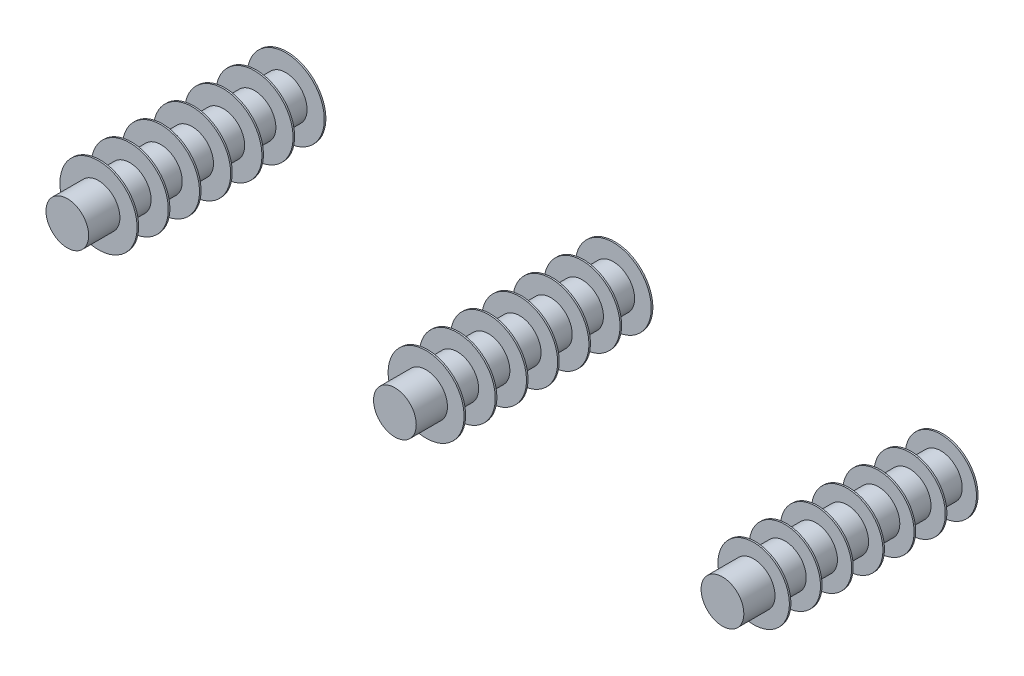
SolidWorks part; units mm, degrees
ref_plane "Alzado" through (0, 0, 0) normal (0, 0, 1) x (1, 0, 0)
ref_plane "Planta" through (0, 0, 0) normal (0, 1, 0) x (1, 0, 0)
ref_plane "Vista lateral" through (0, 0, 0) normal (1, 0, 0) x (0, 0, -1)
sketch "Croquis1" plane through (0, 0, 0) normal (0, 0, 1) x (1, 0, 0)
  line L0 (0, 0) -> (210, 0) construction
  line L1 (210, 0) -> (420, 0) construction
  circle A0 centre (0, 0) radius 13.7
  circle A1 centre (210, 0) radius 13.7
  circle A2 centre (210, 0) radius 13.7
  dimension "D1" = 27.4
  dimension "D3" = 27.4
  dimension "D2" = 210
  dimension "D4" = 210
sketch3d "Croquis3D1"
  line L0 (0, 0, 0) -> (0, 0, 170)
  line L1 (30, 0, 200) -> (145.0002, 0, 200)
  line L2 (175.0002, 0, 230) -> (175.0002, 0, 500)
  line L3 (175.0002, -20, 520) -> (175.0002, -156.8001, 520)
  arc A0 (0, 0, 170) -> (30, 0, 200) centre (30, 0, 170) ccw
  arc A1 (145.0002, 0, 200) -> (175.0002, 0, 230) centre (145.0002, 0, 230) ccw
  arc A2 (175.0002, 0, 500) -> (175.0002, -20, 520) centre (175.0002, -20, 500) ccw
  point P10 (0, 0, 200)
  point P11 (30, 30, 170)
  point P14 (175.0002, 0, 200)
  point P15 (145.0002, -30, 230)
  point P19 (175.0002, 0, 520)
  point P20 (195.0002, -20, 500)
  dimension "D1" = 30
  dimension "D2" = 20
  dimension "D3" = 175.0002
  dimension "D4" = 200
  dimension "D5" = 320
sweep "Barrer5" add path "Croquis3D1" circular profile diameter 27.4 parameters "D3"=27.4
sketch "Croquis14" plane through (0, 0, 0) normal (0, 0, 1) x (1, 0, 0)
  circle A0 centre (210, 0) radius 13.7
sketch3d "Croquis3D2"
  line L0 (210, 0, 0) -> (210, 0, 499.997)
  line L1 (210, -20, 519.997) -> (210, -153.4253, 519.997)
  arc A0 (210, 0, 499.997) -> (210, -20, 519.997) centre (210, -20, 499.997) ccw
  point P8 (210, 0, 519.997)
  point P9 (230, -20, 499.997)
  dimension "D1" = 20
  dimension "D2" = 519.997
sweep "Barrer6" add path "Croquis3D2" circular profile diameter 27.4 parameters "D3"=27.4
sketch "Croquis41" plane through (0, 0, 0) normal (0, 0, -1) x (-1, 0, 0)
  circle A0 centre (-420, 0) radius 13.7
  dimension "D1" = 27.4
sketch3d "Croquis3D3"
  line L0 (420, 0, 0) -> (420, 0, 180)
  line L1 (400, 0, 200) -> (264.998, 0, 200)
  line L2 (244.998, 0, 220) -> (244.998, 0, 500)
  line L3 (244.998, -20, 520) -> (244.998, -158.8149, 520)
  arc A0 (244.998, 0, 500) -> (244.998, -20, 520) centre (244.998, -20, 500) ccw
  arc A1 (420, 0, 180) -> (400, 0, 200) centre (400, 0, 180) ccw
  arc A2 (264.998, 0, 200) -> (244.998, 0, 220) centre (264.998, 0, 220) ccw
  point P8 (244.998, 0, 520)
  point P9 (264.998, -20, 500)
  point P12 (420, 0, 200)
  point P13 (400, -20, 180)
  point P16 (244.998, 0, 200)
  point P17 (264.998, 20, 220)
  dimension "D1" = 20
  dimension "D2" = 175.002
  dimension "D3" = 200
  dimension "D4" = 320
sweep "Barrer7" add profiles "Croquis41" path "Croquis3D3"
sketch "Croquis62" plane through (0, 0, 0) normal (0, 0, -1) x (-1, 0, 0)
  circle A0 centre (-420, 0) radius 22.8702
  circle A1 centre (-210, 0) radius 24.3657
  circle A2 centre (0, 0) radius 24.738
extrude "Saliente-Extruir1" add sketch "Croquis62" along normal blind 1
pattern_linear "MatrizL1" count 7 spacing 20 along (0, 0, 1) of "Saliente-Extruir1"
sketch "Croquis63" plane through (0, -158.8149, 0) normal (0, -1, 0) x (1, 0, 0)
  line L0 (231.298, 520) -> (258.698, 520) construction
  line L1 (258.698, 520) -> (244.998, 520) construction
  line L2 (244.998, 520) -> (244.998, 533.7) construction
  circle A0 centre (244.998, 520) radius 13.7 construction
ref_plane "Plano1" through (0, 0, 520) normal (0, 0, -1) x (1, 0, 0)
sketch "Croquis64" plane through (0, -156.8001, 0) normal (0, -1, 0) x (1, 0, 0)
  circle A0 centre (175.0002, 520) radius 13.7
  circle A1 centre (210, 519.997) radius 13.7
  circle A2 centre (244.998, 520) radius 13.7
ref_plane "Plano2" through (0, 0, 590) normal (0, 0, 1) x (1, 0, 0)
sketch "Croquis73" plane through (0, 0, 590) normal (0, 0, 1) x (1, 0, 0)
  line L1 (-18.8749, 95.4392) -> (455.6283, 95.4392)
  line L2 (-18.8749, 95.4392) -> (-18.8749, -176.4617)
  line L3 (-18.8749, -176.4617) -> (455.6283, -176.4617)
  line L4 (455.6283, 95.4392) -> (455.6283, -176.4617)
  line L5 (-18.8749, 95.4392) -> (455.6283, -176.4617) construction
  line L6 (-18.8749, -176.4617) -> (455.6283, 95.4392) construction
  point P0 (218.3767, -40.5113)
extrude "Cortar-Extruir2" cut sketch "Croquis73" against normal blind 450
sketch3d "Croquis3D4"
  line L0 (175.0002, -156.8001, 520) -> (175.0002, -328.3979, 520)
  line L1 (175.0002, -348.3979, 540) -> (175.0002, -348.3979, 534.5871)
  line L2 (175.0002, -368.3979, 554.5871) -> (175.0002, -536.3535, 554.5871)
  arc A0 (175.0002, -348.3979, 534.5871) -> (175.0002, -368.3979, 554.5871) centre (175.0002, -368.3979, 534.5871) ccw
  arc A1 (175.0002, -328.3979, 520) -> (175.0002, -348.3979, 540) centre (175.0002, -328.3979, 540) ccw
  point P7 (175.0002, -348.3979, 554.5871)
  point P8 (195.0002, -368.3979, 534.5871)
  point P11 (175.0002, -348.3979, 520)
  point P12 (155.0002, -328.3979, 540)
  dimension "D1" = 20
